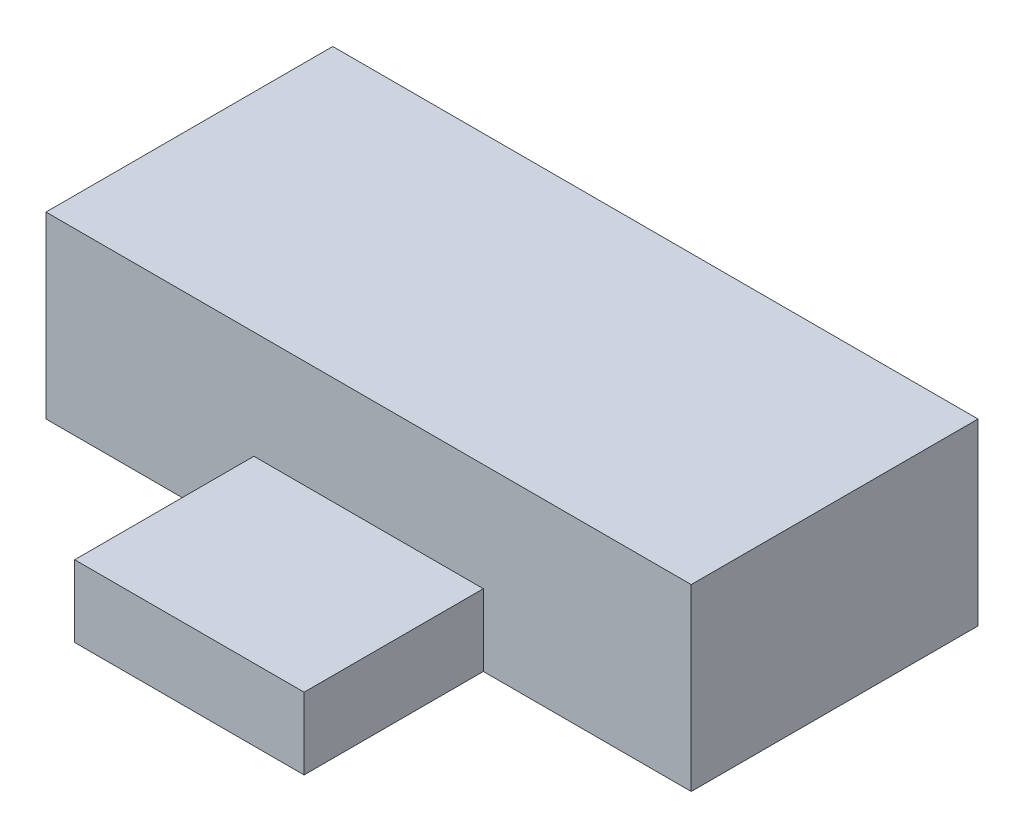
SolidWorks part; units mm, degrees
ref_plane "Plan de face" through (0, 0, 0) normal (0, 0, 1) x (1, 0, 0)
ref_plane "Plan de dessus" through (0, 0, 0) normal (0, 1, 0) x (1, 0, 0)
ref_plane "Plan de droite" through (0, 0, 0) normal (1, 0, 0) x (0, 0, -1)
sketch "Esquisse1" plane through (0, 0, 0) normal (0, 1, 0) x (1, 0, 0)
  line L1 (-9, 4) -> (9, 4)
  line L2 (-9, 4) -> (-9, -4)
  line L3 (-9, -4) -> (9, -4)
  line L4 (9, 4) -> (9, -4)
  line L5 (-9, 4) -> (9, -4) construction
  line L6 (-9, -4) -> (9, 4) construction
  point P0 (0, 0)
  dimension "D1" = 18
  dimension "D2" = 8
extrude "Boss.-Extru.1" add sketch "Esquisse1" along normal blind 5
sketch "Esquisse2" plane through (0, 0, 4) normal (0, 0, 1) x (1, 0, 0)
  line L0 (0, 1) -> (0, 0) construction
  line L1 (-3.2, 2) -> (3.2, 2)
  line L2 (-3.2, 2) -> (-3.2, 0)
  line L3 (-3.2, 0) -> (3.2, 0)
  line L4 (3.2, 2) -> (3.2, 0)
  line L5 (-3.2, 2) -> (3.2, 0) construction
  line L6 (-3.2, 0) -> (3.2, 2) construction
  line L7 (-9, 0) -> (9, 0) construction
  point P0 (0, 1)
  dimension "D1" = 2
  dimension "D2" = 6.4
extrude "Boss.-Extru.2" add sketch "Esquisse2" along normal blind 5
